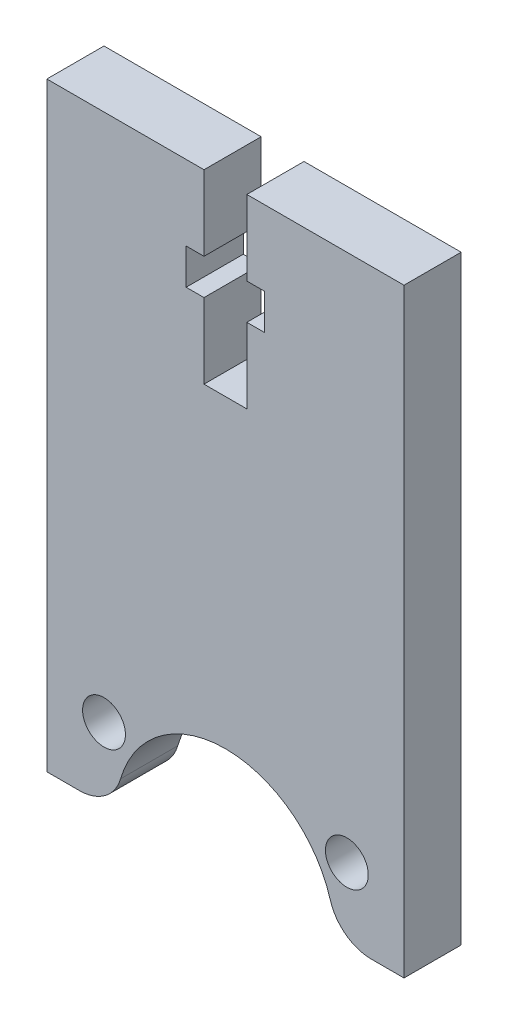
SolidWorks part; units mm, degrees
ref_plane "Спереди" through (0, 0, 0) normal (0, 0, 1) x (1, 0, 0)
ref_plane "Сверху" through (0, 0, 0) normal (0, 1, 0) x (1, 0, 0)
ref_plane "Справа" through (0, 0, 0) normal (1, 0, 0) x (0, 0, -1)
sketch "Эскиз1" plane through (0, 0, 0) normal (0, 0, 1) x (1, 0, 0)
  line L0 (11, 42) -> (11, 36.75)
  line L1 (0, 0) -> (2.2813, 0)
  line L2 (0, 0) -> (0, 42)
  line L3 (0, 42) -> (11, 42)
  line L4 (25, 0) -> (25, 42)
  line L5 (11, 34.25) -> (9.75, 34.25)
  line L6 (9.75, 34.25) -> (9.75, 36.75)
  line L7 (9.75, 36.75) -> (11, 36.75)
  line L8 (11, 34.25) -> (11, 29)
  line L9 (11, 29) -> (14, 29)
  line L10 (22.7187, 0) -> (25, 0)
  line L11 (14, 34.25) -> (14, 29)
  line L12 (14, 34.25) -> (15.25, 34.25)
  line L13 (15.25, 34.25) -> (15.25, 36.75)
  line L14 (15.25, 36.75) -> (14, 36.75)
  line L15 (14, 42) -> (14, 36.75)
  line L16 (14, 42) -> (25, 42)
  circle A0 centre (4, 5) radius 1.5
  circle A1 centre (21, 5) radius 1.5
  arc A2 (19.8402, 2.1549) -> (5.1598, 2.1549) centre (12.5, 0) ccw
  arc A3 (19.8402, 2.1549) -> (22.7187, 0) centre (22.7187, 3) ccw
  arc A4 (5.1598, 2.1549) -> (2.2813, 0) centre (2.2813, 3) cw
  point P26 (20.15, 0)
  dimension "D3" = 3
  dimension "D4" = 5
  dimension "D5" = 17
  dimension "D6" = 5
  dimension "D7" = 4
  dimension "D10" = 15.3
  dimension "D11" = 3
  dimension "D1" = 25
  dimension "D2" = 42
  dimension "D8" = 13
  dimension "D9" = 2.5
extrude "Бобышка-Вытянуть1" add sketch "Эскиз1" along normal blind 4
